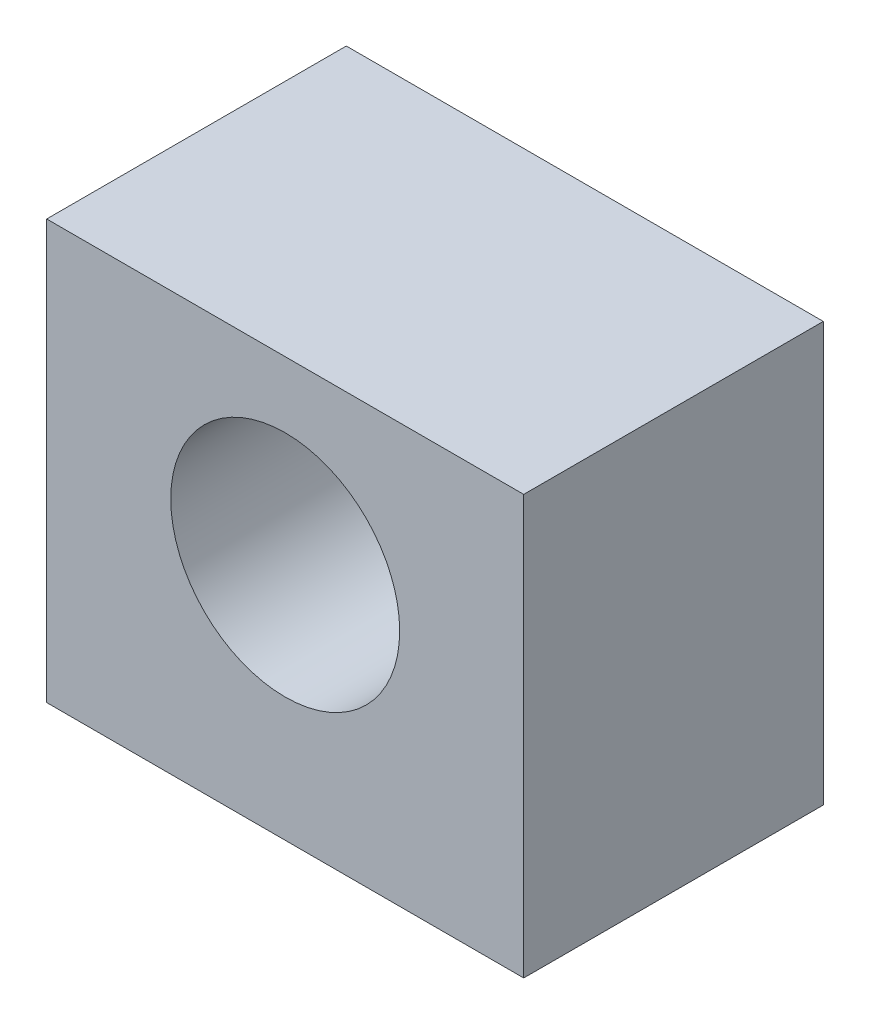
SolidWorks part; units mm, degrees
ref_plane "Front Plane" through (0, 0, 0) normal (0, 0, 1) x (1, 0, 0)
ref_plane "Top Plane" through (0, 0, 0) normal (0, 1, 0) x (1, 0, 0)
ref_plane "Right Plane" through (0, 0, 0) normal (1, 0, 0) x (0, 0, -1)
sketch "Sketch1" plane through (0, 0, 0) normal (0, 0, 1) x (1, 0, 0)
  line L0 (0, 0) -> (3, 0) construction
  line L1 (55, 0) -> (-55, 0) construction
  line L2 (-0.1, -0.1) -> (3, -0.1)
  line L3 (3, 0) -> (7, 0) construction
  line L4 (3, -0.1) -> (7, -0.1)
  line L5 (7, 0) -> (8, 0) construction
  line L6 (8, 0) -> (8, 7) construction
  line L7 (8, 7) -> (0, 7) construction
  line L8 (0, -55) -> (0, 55) construction
  line L9 (0, 7) -> (0, 0) construction
  line L10 (7, -0.1) -> (8.1, -0.1)
  line L11 (8.1, -0.1) -> (8.1, 7.1)
  line L12 (8.1, 7.1) -> (-0.1, 7.1)
  line L13 (-0.1, 7.1) -> (-0.1, -0.1)
  dimension "D1" = 8
  dimension "D2" = 0.1
  dimension "D4" = 7
extrude "Boss-Extrude1" add sketch "Sketch1" along normal blind 5.15
sketch "Sketch2" plane through (0, 0, 5.15) normal (0, 0, 1) x (1, 0, 0)
  line L0 (0, 0) -> (8, 0) construction
  line L1 (4, 0) -> (4, 7) construction
  line L2 (8, 7) -> (0, 7) construction
  circle A0 centre (4, 4) radius 2.0675 construction
  circle A1 centre (4, 4) radius 1.9675
  dimension "D1" = 0.1
extrude "Cut-Extrude1" cut sketch "Sketch2" against normal through all
